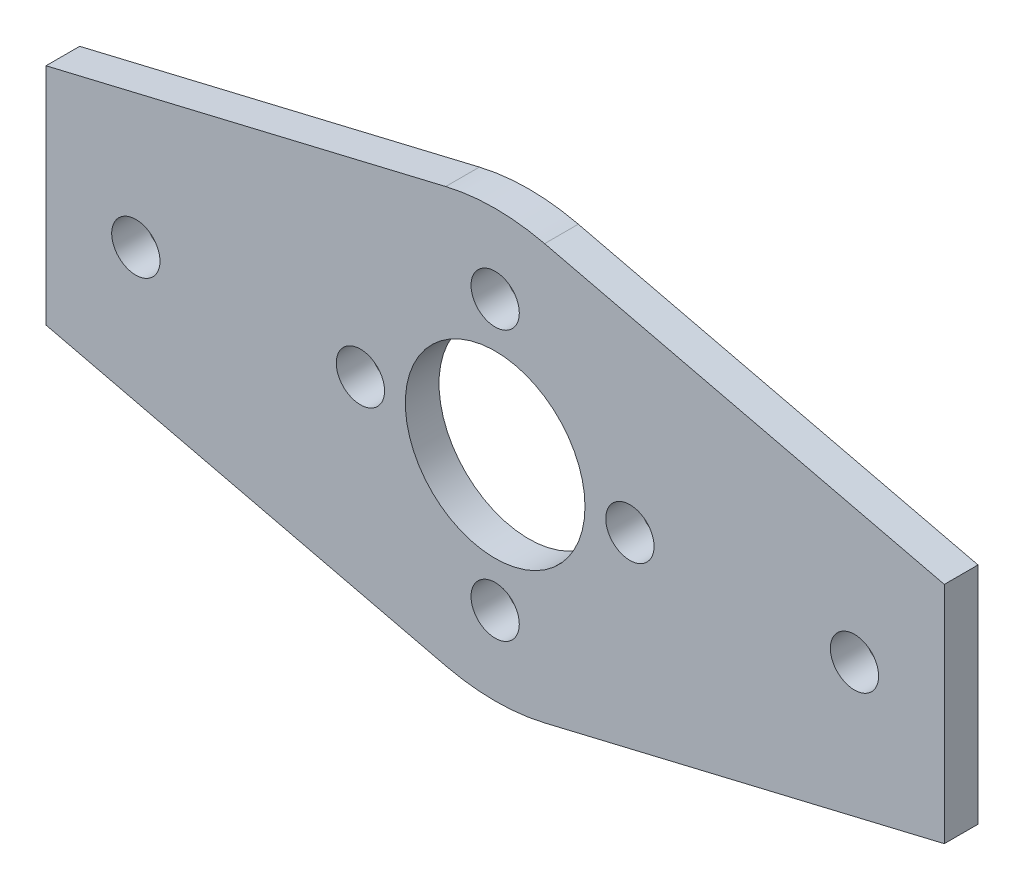
SolidWorks part; units mm, degrees
material "Thornel Mat VMA"
ref_plane "Front Plane" through (0, 0, 0) normal (0, 0, 1) x (1, 0, 0)
ref_plane "Top Plane" through (0, 0, 0) normal (0, 1, 0) x (1, 0, 0)
ref_plane "Right Plane" through (0, 0, 0) normal (1, 0, 0) x (0, 0, -1)
sketch "Sketch1" plane through (0, 0, 0) normal (0, 0, 1) x (1, 0, 0)
  line L0 (-65.3658, -264.7418) -> (-65.3658, -284.7418)
  line L1 (-380.3658, -264.7418) -> (329.6342, -264.7418) construction
  line L2 (-400.3658, -284.7418) -> (349.6342, -284.7418) construction
  line L3 (-65.3658, -264.7418) -> (-29.7702, -256.2594)
  line L4 (-65.3658, -284.7418) -> (-29.7702, -293.2243)
  line L5 (-25.3658, -255.7418) -> (-25.3658, -293.7418) construction
  line L6 (14.6342, -284.7418) -> (-20.9614, -293.2243)
  line L7 (14.6342, -264.7418) -> (-20.9614, -256.2594)
  line L8 (14.6342, -264.7418) -> (14.6342, -284.7418)
  line L9 (14.6342, -284.7418) -> (-20.9614, -293.2243)
  line L10 (14.6342, -264.7418) -> (14.6342, -284.7418)
  line L11 (14.6342, -264.7418) -> (-20.9614, -256.2594)
  line L12 (-65.3658, -264.7418) -> (-29.7702, -256.2594)
  line L13 (-65.3658, -264.7418) -> (-65.3658, -284.7418)
  line L14 (-65.3658, -284.7418) -> (-29.7702, -293.2243)
  arc A0 (-29.7702, -293.2243) -> (-20.9614, -293.2243) centre (-25.3658, -274.7418) ccw
  circle A1 centre (-57.3658, -274.7418) radius 2.15
  circle A2 centre (-37.3658, -274.7418) radius 2.15
  arc A3 (-20.9614, -256.2594) -> (-29.7702, -256.2594) centre (-25.3658, -274.7418) ccw
  circle A4 centre (-13.3658, -274.7418) radius 2.15
  circle A5 centre (6.6342, -274.7418) radius 2.15
  circle A6 centre (-25.3658, -274.7418) radius 8 construction
  circle A7 centre (-25.3658, -274.7418) radius 8
  circle A8 centre (-25.3658, -262.7418) radius 2.15
  circle A9 centre (-25.3658, -286.7418) radius 2.15
  dimension "D1" = 38
  dimension "D3" = 12
  dimension "D4" = 4.3
  dimension "D5" = 8
  dimension "D6" = 4.3
  dimension "D7" = 12
  dimension "D2" = 40
  dimension "D8" = 12
extrude "Extrude1" add sketch "Sketch1" along normal blind 3 contours L5 A3 L3 L0 L4 A0 A7 A1 A2 | A3 L5 A7 A0 L6 L8 L7 A5 A4
